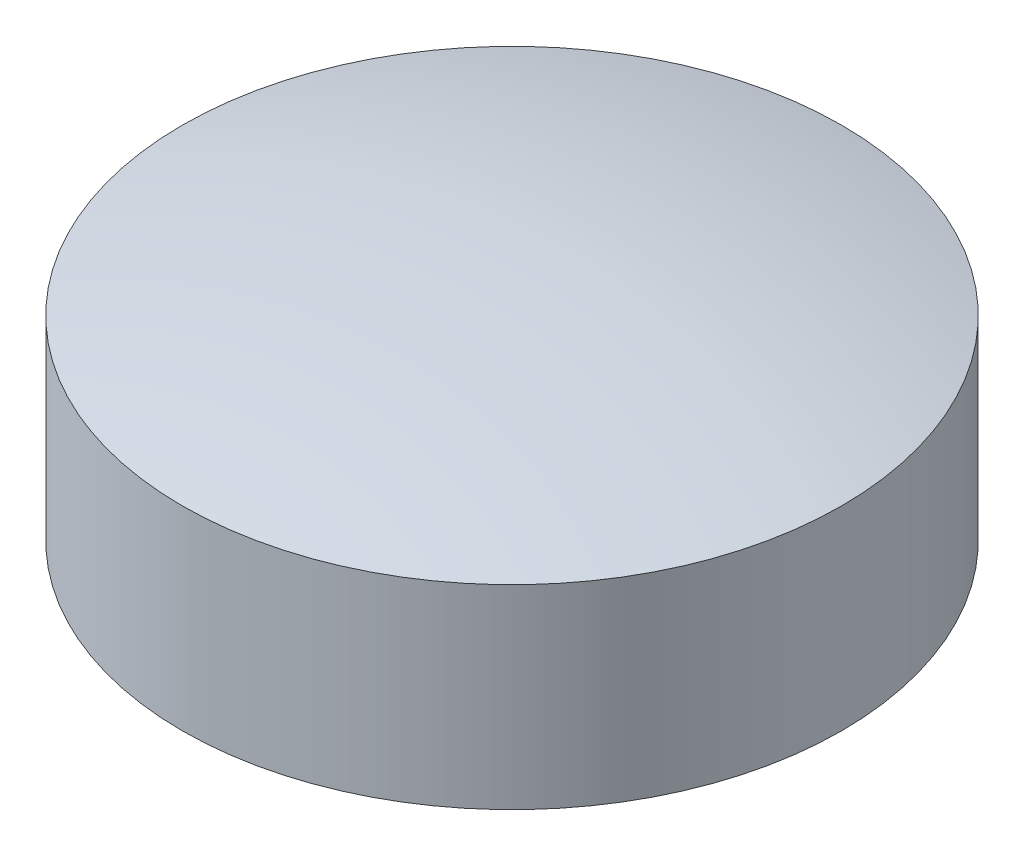
SolidWorks part; units mm, degrees
ref_plane "Front Plane" through (0, 0, 0) normal (0, 0, 1) x (1, 0, 0)
ref_plane "Top Plane" through (0, 0, 0) normal (0, 1, 0) x (1, 0, 0)
ref_plane "Right Plane" through (0, 0, 0) normal (1, 0, 0) x (0, 0, -1)
sketch "Sketch2" plane through (0, 0, 0) normal (0, 0, 1) x (1, 0, 0)
  line L0 (0, 0) -> (0, 128.2) construction
  line L1 (0, 0) -> (22, 0)
  line L2 (22, 0) -> (22, 13)
  line L4 (0, 16) -> (0, 0)
  arc A0 (0, 16) -> (22, 13) centre (0, -66.1667) cw
  dimension "D1" = 13
  dimension "D2" = 44
  dimension "D3" = 3
revolve "Revolve1" add sketch "Sketch2" angle 360 about L0
sketch "Sketch3" plane through (0, 0, 0) normal (0, 1, 0) x (1, 0, 0)
  circle A0 centre (-22, 0) radius 1.5
  dimension "D1" = 3
  dimension "D2" = 22
extrude "Cut-Extrude1" cut sketch "Sketch3" along normal blind 10
